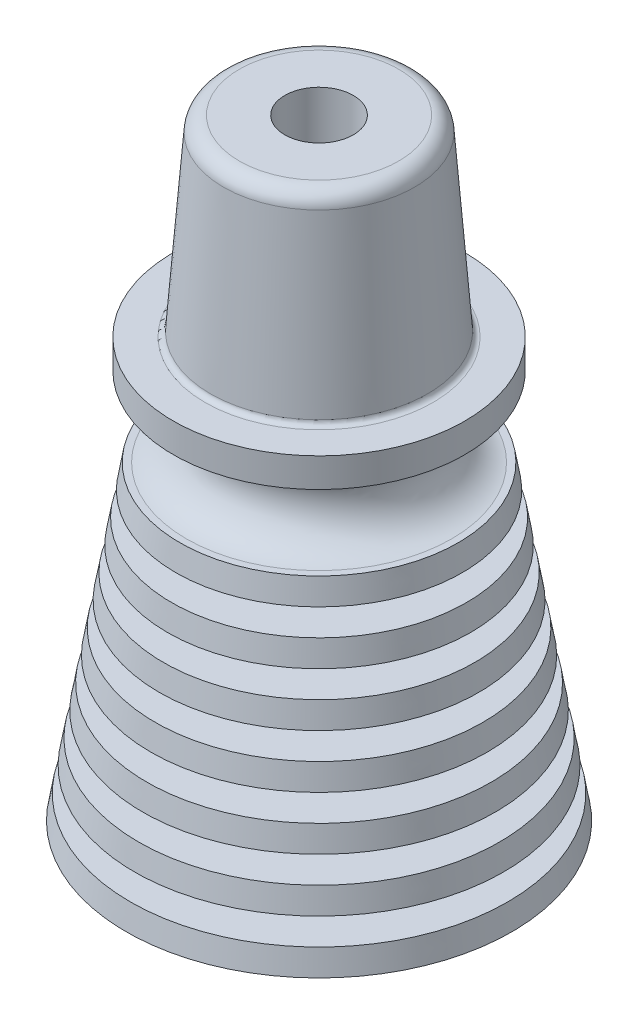
SolidWorks part; units mm, degrees
ref_plane "Front Plane" through (0, 0, 0) normal (0, 0, 1) x (1, 0, 0)
ref_plane "Top Plane" through (0, 0, 0) normal (0, 1, 0) x (1, 0, 0)
ref_plane "Right Plane" through (0, 0, 0) normal (1, 0, 0) x (0, 0, -1)
sketch "Sketch1" plane through (0, 0, 0) normal (0, 0, 1) x (1, 0, 0)
  line L0 (0, 0) -> (0, 105.2466) construction
  line L1 (0, 0) -> (16.8253, 0) construction
  line L2 (2.5273, 14.859) -> (4.191, 0) construction
  line L3 (0, 14.859) -> (9.4545, 14.859) construction
  line L4 (6.6675, 14.859) -> (9.2329, 0) construction
  line L5 (4.572, 14.859) -> (6.2357, 0)
  line L6 (4.5467, 15.0851) -> (6.2104, 0.2261) construction
  line L7 (4.572, 14.859) -> (2.5273, 14.859)
  line L8 (2.5273, 14.859) -> (4.191, 0)
  line L9 (4.191, 0) -> (6.2357, 0)
  circle A0 centre (0, 0) radius 9.2329 construction
  circle A1 centre (0, 14.859) radius 6.6675 construction
  circle A2 centre (0, 0) radius 4.191 construction
  circle A3 centre (0, 14.859) radius 2.5273 construction
  dimension "D1" = 18.4658
  dimension "D3" = 13.335
  dimension "D4" = 8.382
  dimension "D5" = 5.0546
  dimension "D2" = 14.859
  dimension "D6" = 2.032
revolve "Revolve1" add sketch "Sketch1" angle 360 about L0
sketch "Sketch2" plane through (0, 0, 0) normal (0, 0, 1) x (1, 0, 0)
  line L0 (0, 0) -> (16.8253, 0) construction
  line L1 (6.6675, 14.859) -> (9.2329, 0) construction
  line L2 (4.572, 14.859) -> (6.2357, 0) construction
  line L4 (6.2357, 0) -> (9.2329, 0)
  line L5 (9.0356, 1.143) -> (9.2329, 0)
  line L6 (6.1077, 1.143) -> (6.2357, 0)
  line L7 (6.1077, 1.143) -> (9.0356, 1.143)
  line L8 (4.572, 14.859) -> (4.7, 13.716)
  line L9 (6.6675, 14.859) -> (6.8648, 13.716)
  line L10 (5.9797, 2.286) -> (8.8382, 2.286)
  line L11 (5.8518, 3.429) -> (8.6409, 3.429)
  line L12 (5.7238, 4.572) -> (8.4435, 4.572)
  line L13 (5.5958, 5.715) -> (8.2462, 5.715)
  line L14 (5.4678, 6.858) -> (8.0489, 6.858)
  line L15 (5.3399, 8.001) -> (7.8515, 8.001)
  line L16 (8.2462, 5.715) -> (8.4435, 4.572)
  line L17 (5.5958, 5.715) -> (5.7238, 4.572)
  line L18 (5.8518, 3.429) -> (5.9797, 2.286)
  line L19 (8.6409, 3.429) -> (8.8382, 2.286)
  line L20 (5.2119, 9.144) -> (7.6542, 9.144)
  line L21 (5.0839, 10.287) -> (7.4569, 10.287)
  line L22 (4.9559, 11.43) -> (7.2595, 11.43)
  line L23 (4.828, 12.573) -> (7.0622, 12.573)
  line L24 (7.8515, 8.001) -> (8.0489, 6.858)
  line L25 (5.3399, 8.001) -> (5.4678, 6.858)
  line L26 (7.4569, 10.287) -> (7.6542, 9.144)
  line L27 (5.0839, 10.287) -> (5.2119, 9.144)
  line L28 (4.572, 14.859) -> (6.6675, 14.859)
  line L29 (4.7, 13.716) -> (6.8648, 13.716)
  line L30 (4.828, 12.573) -> (4.9559, 11.43)
  line L31 (7.0622, 12.573) -> (7.2595, 11.43)
  dimension "D1" = 1.143
  dimension "D2" = 1.143
  dimension "D3" = 2.286
  dimension "D4" = 1.143
  dimension "D5" = 2.286
  dimension "D6" = 1.143
  dimension "D7" = 2.286
  dimension "D8" = 1.143
  dimension "D9" = 2.286
  dimension "D10" = 2.286
  dimension "D11" = 1.143
  dimension "D12" = 1.143
revolve "Revolve2" add sketch "Sketch2" angle 360 about L0
sketch "Sketch3" plane through (0, 0, 0) normal (0, 0, 1) x (1, 0, 0)
  line L0 (6.6675, 14.859) -> (-6.6675, 14.859) construction
  line L1 (6.35, 14.859) -> (0, 14.859)
  line L2 (0, 0) -> (0, 26.3541) construction
  line L4 (6.35, 18.669) -> (6.985, 18.669)
  line L5 (0, 20.066) -> (6.985, 20.066)
  line L6 (6.985, 20.066) -> (6.985, 18.669)
  line L7 (-9.2329, 0) -> (9.2329, 0) construction
  line L8 (6.35, 18.669) -> (6.35, 14.859) construction
  line L9 (0, 20.066) -> (0, 14.859)
  arc A0 (6.35, 18.669) -> (6.35, 14.859) centre (6.6088, 16.764) ccw
  dimension "D5" = 9.3726
  dimension "D1" = 1.397
  dimension "D2" = 20.066
  dimension "D3" = 13.97
  dimension "D4" = 0.635
revolve "Revolve3" add sketch "Sketch3" angle 360 about L2
sketch "Sketch4" plane through (0, 0, 0) normal (0, 0, 1) x (1, 0, 0)
  line L0 (0, 0) -> (0, 32.0807) construction
  line L1 (6.985, 20.066) -> (-6.985, 20.066) construction
  line L2 (5.2197, 20.066) -> (0, 20.066)
  line L3 (0, 29.2608) -> (4.5212, 29.2608)
  line L4 (4.5212, 29.2608) -> (5.2197, 20.066)
  line L5 (0, 20.066) -> (0, 29.2608)
  line L6 (-9.2329, 0) -> (9.2329, 0) construction
  dimension "D1" = 9.0424
  dimension "D2" = 10.4394
  dimension "D3" = 29.2608
revolve "Revolve4" add sketch "Sketch4" angle 360 about L0
sketch "Sketch5" plane through (0, 29.2608, 0) normal (0, 1, 0) x (1, 0, 0)
  circle A0 centre (0, 0) radius 1.6383
  dimension "D1" = 3.2766
extrude "Cut-Extrude1" cut sketch "Sketch5" against normal through all
fillet "Fillet1" radius 0.762 1 edges at (0, 29.2608, -4.5212)
fillet "Fillet2" radius 0.254 1 edges at (0, 20.066, 5.2197)
ref_plane "Plane1" through (0, 16.764, 0) normal (0, -1, 0) x (-1, 0, 0)
sketch "Sketch6" plane through (0, 16.764, 0) normal (0, -1, 0) x (-1, 0, 0)
  circle A0 centre (0, 0) radius 7.62 construction
  dimension "D1" = 15.24
